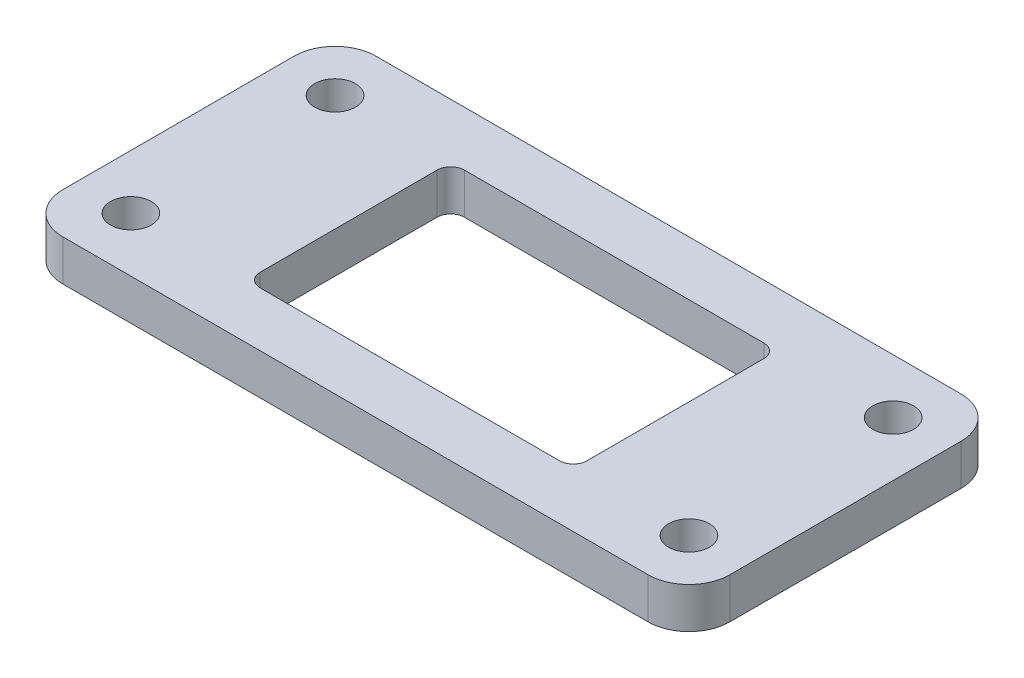
SolidWorks part; units mm, degrees
ref_plane "Front Plane" through (0, 0, 0) normal (0, 0, 1) x (1, 0, 0)
ref_plane "Top Plane" through (0, 0, 0) normal (0, 1, 0) x (1, 0, 0)
ref_plane "Right Plane" through (0, 0, 0) normal (1, 0, 0) x (0, 0, -1)
sketch "Sketch1" plane through (0, 0, 0) normal (0, 1, 0) x (1, 0, 0)
  line L0 (20.5, -30.883) -> (20.5, 23.5642) construction
  line L1 (-4, 1) -> (-4, -16)
  line L2 (-1, 4) -> (42, 4)
  line L5 (45, 1) -> (45, -16)
  line L14 (-1, -19) -> (42, -19)
  line L16 (9.5, 0) -> (31.5, 0)
  line L17 (8.5, -1) -> (8.5, -14)
  line L18 (9.5, -15) -> (15.8808, -15)
  line L19 (32.5, -1) -> (32.5, -14)
  line L22 (15.8808, -15) -> (31.5, -15)
  circle A0 centre (0, 0) radius 1.5
  circle A1 centre (41, 0) radius 1.5
  circle A2 centre (41, -15) radius 1.5
  arc A3 (-1, -19) -> (-4, -16) centre (-1, -16) cw
  circle A4 centre (0, -15) radius 1.5
  arc A9 (42, 4) -> (45, 1) centre (42, 1) cw
  arc A10 (-1, 4) -> (-4, 1) centre (-1, 1) ccw
  arc A12 (42, -19) -> (45, -16) centre (42, -16) ccw
  arc A13 (8.5, -14) -> (9.5, -15) centre (9.5, -14) ccw
  arc A14 (9.5, 0) -> (8.5, -1) centre (9.5, -1) ccw
  arc A15 (31.5, 0) -> (32.5, -1) centre (31.5, -1) cw
  arc A16 (31.5, -15) -> (32.5, -14) centre (31.5, -14) ccw
  point P51 (20.5, -23.147)
  dimension "D1" = 3
  dimension "D2" = 41
  dimension "D9" = 4
  dimension "D4" = 3
  dimension "D11" = 4
  dimension "D14" = 3
  dimension "D15" = 1
  dimension "D5" = 3
  dimension "D3" = 15
  dimension "D6" = 4
  dimension "D7" = 4
  dimension "D8" = 4
extrude "Boss-Extrude1" add sketch "Sketch1" along normal blind 3
